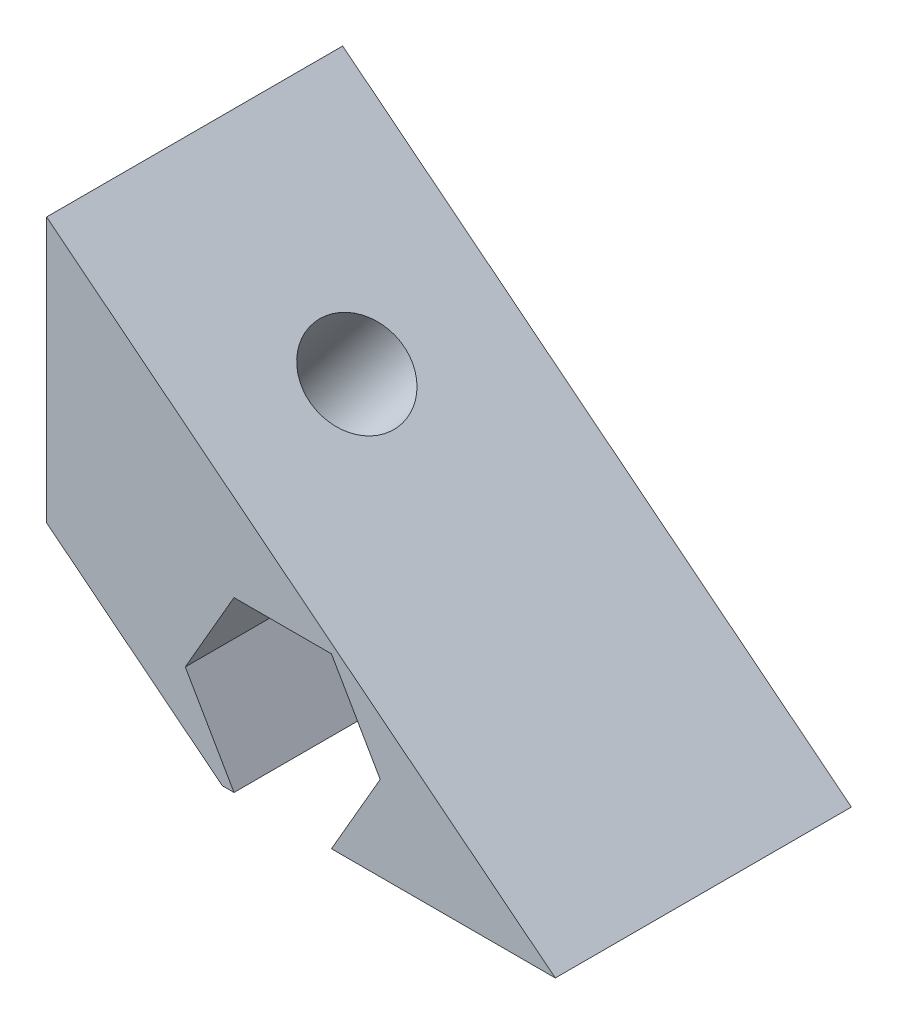
SolidWorks part; units mm, degrees
ref_plane "Alzado" through (0, 0, 0) normal (0, 0, 1) x (1, 0, 0)
ref_plane "Planta" through (0, 0, 0) normal (0, 1, 0) x (1, 0, 0)
ref_plane "Vista lateral" through (0, 0, 0) normal (1, 0, 0) x (0, 0, -1)
sketch "Croquis1" plane through (0, 0, 0) normal (0, 0, 1) x (1, 0, 0)
  line L0 (0, 0) -> (22, 0) construction
  line L1 (22, 0) -> (0, 17.5) construction
  line L2 (0, 17.5) -> (0, 0) construction
  line L3 (17.1809, 0) -> (0, 13.6666) construction
  line L4 (17.1809, 0) -> (5.9364, 0)
  line L5 (5.9364, 0) -> (0, 4.7221)
  line L6 (0, 4.7221) -> (0, 13.6666)
  line L7 (0, 13.6666) -> (17.1809, 0)
  line L8 (0, 0) -> (8.5258, 10.7181) construction
  line L9 (0, 9.1944) -> (11.5586, 0) construction
  circle A0 centre (7.9758, 2.85) radius 1.6
  dimension "D5" = 3.2
  dimension "D1" = 17.5
  dimension "D2" = 22
  dimension "D3" = 3
  dimension "D4" = 7
  dimension "D6" = 2.85
extrude "Saliente-Extruir1" add sketch "Croquis1" along normal blind 10
sketch "Croquis2" plane through (0, 0, 10) normal (0, 0, 1) x (1, 0, 0)
  line L1 (6.3303, 0) -> (9.6212, 0)
  line L2 (9.6212, 0) -> (11.2667, 2.85)
  line L3 (11.2667, 2.85) -> (9.6212, 5.7)
  line L4 (9.6212, 5.7) -> (6.3303, 5.7)
  line L5 (6.3303, 5.7) -> (4.6849, 2.85)
  line L6 (4.6849, 2.85) -> (6.3303, 0)
  line L7 (5.9364, 0) -> (17.1809, 0) construction
  circle A0 centre (7.9758, 2.85) radius 2.85 construction
  dimension "D1" = 5.7
extrude "Cortar-Extruir1" cut sketch "Croquis2" against normal offset from surface (5.5 mm away) 4.5 up to face at (5.7793, 4.5972, 0)
sketch "Croquis3" plane through (6.6582, 8.3703, 0) normal (0.6225, 0.7826, 0) x (0.7826, -0.6225, 0)
  line L0 (-8.5078, -5) -> (13.4458, -5) construction
  line L1 (-8.5078, -10) -> (-8.5078, 0) construction
  line L2 (13.4458, -10) -> (13.4458, 0) construction
  circle A0 centre (-1.5078, -5) radius 1.6
  dimension "D1" = 3.2
  dimension "D2" = 7
extrude "Cortar-Extruir2" cut sketch "Croquis3" against normal up to next
sketch "Croquis4" plane through (2.3005, 2.8921, 0) normal (-0.6225, -0.7826, 0) x (0.7826, -0.6225, 0)
  line L1 (1.7831, 5) -> (0.1376, 7.85)
  line L2 (0.1376, 7.85) -> (-3.1532, 7.85)
  line L3 (-3.1532, 7.85) -> (-4.7987, 5)
  line L4 (-4.7987, 5) -> (-3.1532, 2.15)
  line L5 (-3.1532, 2.15) -> (0.1376, 2.15)
  line L6 (0.1376, 2.15) -> (1.7831, 5)
  circle A0 centre (-1.5078, 5) radius 2.85 construction
  dimension "D1" = 5.7
extrude "Cortar-Extruir3" cut sketch "Croquis4" against normal offset from surface (2.5 mm away) 4.5 up to face at (4.226, 10.305, 5)
